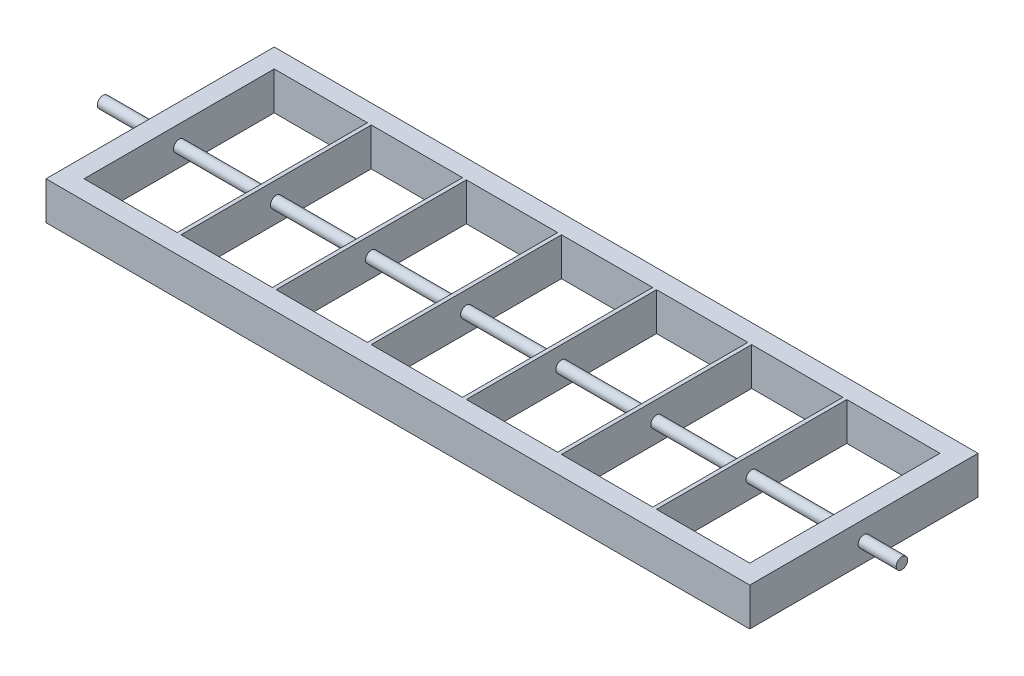
SolidWorks part; units mm, degrees
ref_plane "Front Plane" through (0, 0, 0) normal (0, 0, 1) x (1, 0, 0)
ref_plane "Top Plane" through (0, 0, 0) normal (0, 1, 0) x (1, 0, 0)
ref_plane "Right Plane" through (0, 0, 0) normal (1, 0, 0) x (0, 0, -1)
sketch "Sketch1" plane through (0, 0, 0) normal (0, 1, 0) x (1, 0, 0)
  line L0 (-175, 50) -> (175, 50)
  line L1 (-185, -60) -> (185, -60)
  line L2 (-185, -60) -> (-185, 60)
  line L3 (-185, 60) -> (185, 60)
  line L4 (185, -60) -> (185, 60)
  line L5 (-185, -60) -> (185, 60) construction
  line L6 (-185, 60) -> (185, -60) construction
  line L7 (175, -50) -> (175, 50)
  line L8 (-175, -50) -> (175, -50)
  line L9 (-175, -50) -> (-175, 50)
  point P0 (0, 0)
  dimension "D1" = 370
  dimension "D2" = 120
  dimension "D3" = 10
extrude "Boss-Extrude1" add sketch "Sketch1" along normal blind 20
sketch "Sketch2" plane through (-185, 0, 0) normal (-1, 0, 0) x (0, 0, 1)
  circle A0 centre (0, 10) radius 3
  dimension "D2" = 6
  dimension "D1" = 10
extrude "Boss-Extrude2" add sketch "Sketch2" along normal blind 30 and the other way blind 390
sketch "Sketch4" plane through (0, 0, 50) normal (0, 0, -1) x (-1, 0, 0)
  line L0 (-126, 20) -> (-124, 20)
  line L3 (-126, 20) -> (-126, 0)
  line L4 (-124, 20) -> (-124, 0)
  line L5 (-126, 0) -> (-124, 0)
  line L6 (-76, 20) -> (-74, 20)
  line L7 (-76, 20) -> (-76, 0)
  line L8 (-74, 20) -> (-74, 0)
  line L9 (-26, 20) -> (-24, 20)
  line L10 (-26, 20) -> (-26, 0)
  line L11 (-24, 20) -> (-24, 0)
  line L12 (24, 20) -> (26, 20)
  line L13 (24, 20) -> (24, 0)
  line L14 (26, 20) -> (26, 0)
  line L15 (74, 20) -> (76, 20)
  line L16 (74, 20) -> (74, 0)
  line L17 (76, 20) -> (76, 0)
  line L18 (124, 20) -> (126, 20)
  line L19 (124, 20) -> (124, 0)
  line L20 (126, 20) -> (126, 0)
  line M1 (-175, 0) -> (175, 0)
  line M3 (175, 20) -> (-175, 20)
  dimension "D1" = 6
extrude "Boss-Extrude3" add sketch "Sketch4" along normal up to surface (100 mm away) contours L4 L3 M3 M1 | L8 L7 M3 M1 | L11 L10 M3 M1 | L14 L13 M3 M1 | L17 L16 M3 M1 | L20 L19 M3 M1 up to face at (0, 10, -50)
